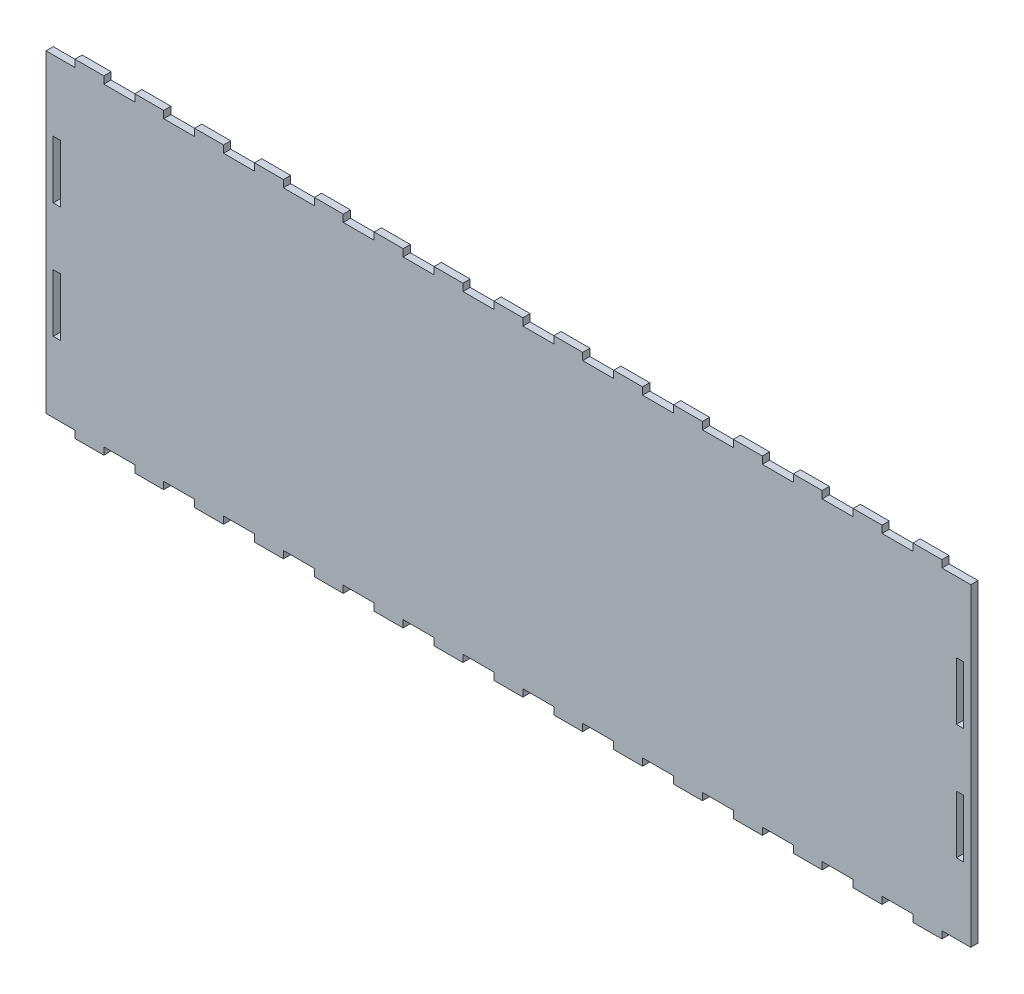
SolidWorks part; units mm, degrees
ref_plane "Front Plane" through (0, 0, 0) normal (0, 0, 1) x (1, 0, 0)
ref_plane "Top Plane" through (0, 0, 0) normal (0, 1, 0) x (1, 0, 0)
ref_plane "Right Plane" through (0, 0, 0) normal (1, 0, 0) x (0, 0, -1)
sketch "Sketch1" plane through (0, 0, 0) normal (0, 0, 1) x (1, 0, 0)
  line L8 (3.175, 81.7118) -> (6.35, 81.7118)
  line L9 (6.35, 81.7118) -> (6.35, 107.1118)
  line L10 (6.35, 107.1118) -> (3.175, 107.1118)
  line L11 (3.175, 107.1118) -> (3.175, 81.7118)
  line L16 (3.175, 30.9118) -> (6.35, 30.9118)
  line L17 (6.35, 30.9118) -> (6.35, 56.3118)
  line L18 (6.35, 56.3118) -> (3.175, 56.3118)
  line L19 (3.175, 56.3118) -> (3.175, 30.9118)
  line L24 (403.225, 56.3118) -> (400.05, 56.3118)
  line L25 (400.05, 56.3118) -> (400.05, 30.9118)
  line L26 (400.05, 30.9118) -> (403.225, 30.9118)
  line L27 (403.225, 30.9118) -> (403.225, 56.3118)
  line L32 (403.225, 107.1118) -> (400.05, 107.1118)
  line L33 (400.05, 107.1118) -> (400.05, 81.7118)
  line L34 (400.05, 81.7118) -> (403.225, 81.7118)
  line L35 (403.225, 81.7118) -> (403.225, 107.1118)
  line L248 (406.4, 0) -> (406.4, 138.0236)
  line L249 (406.4, 138.0236) -> (393.7, 138.0236)
  line L250 (393.7, 138.0236) -> (393.7, 141.1986)
  line L251 (393.7, 141.1986) -> (381, 141.1986)
  line L252 (381, 141.1986) -> (381, 138.0236)
  line L253 (381, 138.0236) -> (367.3929, 138.0236)
  line L254 (367.3929, 138.0236) -> (367.3929, 141.1986)
  line L255 (367.3929, 141.1986) -> (354.6929, 141.1986)
  line L256 (354.6929, 141.1986) -> (354.6929, 138.0236)
  line L257 (354.6929, 138.0236) -> (341.0857, 138.0236)
  line L258 (341.0857, 138.0236) -> (341.0857, 141.1986)
  line L259 (341.0857, 141.1986) -> (328.3857, 141.1986)
  line L260 (328.3857, 141.1986) -> (328.3857, 138.0236)
  line L261 (328.3857, 138.0236) -> (314.7786, 138.0236)
  line L262 (314.7786, 138.0236) -> (314.7786, 141.1986)
  line L263 (314.7786, 141.1986) -> (302.0786, 141.1986)
  line L264 (302.0786, 141.1986) -> (302.0786, 138.0236)
  line L265 (302.0786, 138.0236) -> (288.4714, 138.0236)
  line L266 (288.4714, 138.0236) -> (288.4714, 141.1986)
  line L267 (288.4714, 141.1986) -> (275.7714, 141.1986)
  line L268 (275.7714, 141.1986) -> (275.7714, 138.0236)
  line L269 (275.7714, 138.0236) -> (262.1643, 138.0236)
  line L270 (262.1643, 138.0236) -> (262.1643, 141.1986)
  line L271 (262.1643, 141.1986) -> (249.4643, 141.1986)
  line L272 (249.4643, 141.1986) -> (249.4643, 138.0236)
  line L273 (249.4643, 138.0236) -> (235.8571, 138.0236)
  line L274 (235.8571, 138.0236) -> (235.8571, 141.1986)
  line L275 (235.8571, 141.1986) -> (223.1571, 141.1986)
  line L276 (223.1571, 141.1986) -> (223.1571, 138.0236)
  line L277 (223.1571, 138.0236) -> (209.55, 138.0236)
  line L278 (209.55, 138.0236) -> (209.55, 141.1986)
  line L279 (209.55, 141.1986) -> (196.85, 141.1986)
  line L280 (196.85, 141.1986) -> (196.85, 138.0236)
  line L281 (196.85, 138.0236) -> (183.2429, 138.0236)
  line L282 (183.2429, 138.0236) -> (183.2429, 141.1986)
  line L283 (183.2429, 141.1986) -> (170.5429, 141.1986)
  line L284 (170.5429, 141.1986) -> (170.5429, 138.0236)
  line L285 (170.5429, 138.0236) -> (156.9357, 138.0236)
  line L286 (156.9357, 138.0236) -> (156.9357, 141.1986)
  line L287 (156.9357, 141.1986) -> (144.2357, 141.1986)
  line L288 (144.2357, 141.1986) -> (144.2357, 138.0236)
  line L289 (144.2357, 138.0236) -> (130.6286, 138.0236)
  line L290 (130.6286, 138.0236) -> (130.6286, 141.1986)
  line L291 (130.6286, 141.1986) -> (117.9286, 141.1986)
  line L292 (117.9286, 141.1986) -> (117.9286, 138.0236)
  line L293 (117.9286, 138.0236) -> (104.3214, 138.0236)
  line L294 (104.3214, 138.0236) -> (104.3214, 141.1986)
  line L295 (104.3214, 141.1986) -> (91.6214, 141.1986)
  line L296 (91.6214, 141.1986) -> (91.6214, 138.0236)
  line L297 (91.6214, 138.0236) -> (78.0143, 138.0236)
  line L298 (78.0143, 138.0236) -> (78.0143, 141.1986)
  line L299 (78.0143, 141.1986) -> (65.3143, 141.1986)
  line L300 (65.3143, 141.1986) -> (65.3143, 138.0236)
  line L301 (65.3143, 138.0236) -> (51.7071, 138.0236)
  line L302 (51.7071, 138.0236) -> (51.7071, 141.1986)
  line L303 (51.7071, 141.1986) -> (39.0071, 141.1986)
  line L304 (39.0071, 141.1986) -> (39.0071, 138.0236)
  line L305 (39.0071, 138.0236) -> (25.4, 138.0236)
  line L306 (25.4, 138.0236) -> (25.4, 141.1986)
  line L307 (25.4, 141.1986) -> (12.7, 141.1986)
  line L308 (12.7, 141.1986) -> (12.7, 138.0236)
  line L309 (12.7, 138.0236) -> (0, 138.0236)
  line L310 (0, 138.0236) -> (0, 0)
  line L311 (0, 0) -> (12.7, 0)
  line L312 (12.7, 0) -> (12.7, -3.175)
  line L313 (12.7, -3.175) -> (25.4, -3.175)
  line L314 (25.4, -3.175) -> (25.4, 0)
  line L315 (25.4, 0) -> (39.0071, 0)
  line L316 (39.0071, 0) -> (39.0071, -3.175)
  line L317 (39.0071, -3.175) -> (51.7071, -3.175)
  line L318 (51.7071, -3.175) -> (51.7071, 0)
  line L319 (51.7071, 0) -> (65.3143, 0)
  line L320 (65.3143, 0) -> (65.3143, -3.175)
  line L321 (65.3143, -3.175) -> (78.0143, -3.175)
  line L322 (78.0143, -3.175) -> (78.0143, 0)
  line L323 (78.0143, 0) -> (91.6214, 0)
  line L324 (91.6214, 0) -> (91.6214, -3.175)
  line L325 (91.6214, -3.175) -> (104.3214, -3.175)
  line L326 (104.3214, -3.175) -> (104.3214, 0)
  line L327 (104.3214, 0) -> (117.9286, 0)
  line L328 (117.9286, 0) -> (117.9286, -3.175)
  line L329 (117.9286, -3.175) -> (130.6286, -3.175)
  line L330 (130.6286, -3.175) -> (130.6286, 0)
  line L331 (130.6286, 0) -> (144.2357, 0)
  line L332 (144.2357, 0) -> (144.2357, -3.175)
  line L333 (144.2357, -3.175) -> (156.9357, -3.175)
  line L334 (156.9357, -3.175) -> (156.9357, 0)
  line L335 (156.9357, 0) -> (170.5429, 0)
  line L336 (170.5429, 0) -> (170.5429, -3.175)
  line L337 (170.5429, -3.175) -> (183.2429, -3.175)
  line L338 (183.2429, -3.175) -> (183.2429, 0)
  line L339 (183.2429, 0) -> (196.85, 0)
  line L340 (196.85, 0) -> (196.85, -3.175)
  line L341 (196.85, -3.175) -> (209.55, -3.175)
  line L342 (209.55, -3.175) -> (209.55, 0)
  line L343 (209.55, 0) -> (223.1571, 0)
  line L344 (223.1571, 0) -> (223.1571, -3.175)
  line L345 (223.1571, -3.175) -> (235.8571, -3.175)
  line L346 (235.8571, -3.175) -> (235.8571, 0)
  line L347 (235.8571, 0) -> (249.4643, 0)
  line L348 (249.4643, 0) -> (249.4643, -3.175)
  line L349 (249.4643, -3.175) -> (262.1643, -3.175)
  line L350 (262.1643, -3.175) -> (262.1643, 0)
  line L351 (262.1643, 0) -> (275.7714, 0)
  line L352 (275.7714, 0) -> (275.7714, -3.175)
  line L353 (275.7714, -3.175) -> (288.4714, -3.175)
  line L354 (288.4714, -3.175) -> (288.4714, 0)
  line L355 (288.4714, 0) -> (302.0786, 0)
  line L356 (302.0786, 0) -> (302.0786, -3.175)
  line L357 (302.0786, -3.175) -> (314.7786, -3.175)
  line L358 (314.7786, -3.175) -> (314.7786, 0)
  line L359 (314.7786, 0) -> (328.3857, 0)
  line L360 (328.3857, 0) -> (328.3857, -3.175)
  line L361 (328.3857, -3.175) -> (341.0857, -3.175)
  line L362 (341.0857, -3.175) -> (341.0857, 0)
  line L363 (341.0857, 0) -> (354.6929, 0)
  line L364 (354.6929, 0) -> (354.6929, -3.175)
  line L365 (354.6929, -3.175) -> (367.3929, -3.175)
  line L366 (367.3929, -3.175) -> (367.3929, 0)
  line L367 (367.3929, 0) -> (381, 0)
  line L368 (381, 0) -> (381, -3.175)
  line L369 (381, -3.175) -> (393.7, -3.175)
  line L370 (393.7, -3.175) -> (393.7, 0)
  line L371 (393.7, 0) -> (406.4, 0)
extrude "Boss-Extrude1" add sketch "Sketch1" along normal blind 3.175
